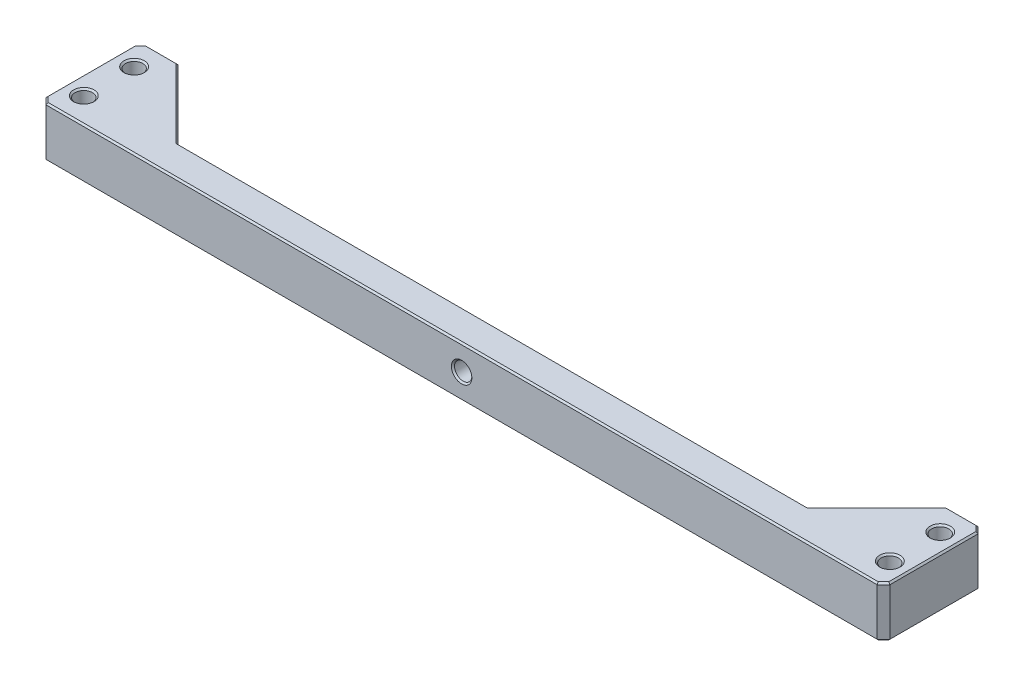
SolidWorks part; units mm, degrees
ref_plane "Front Plane" through (0, 0, 0) normal (0, 0, 1) x (1, 0, 0)
ref_plane "Top Plane" through (0, 0, 0) normal (0, 1, 0) x (1, 0, 0)
ref_plane "Right Plane" through (0, 0, 0) normal (1, 0, 0) x (0, 0, -1)
sketch "Sketch1" plane through (0, 0, 0) normal (0, 1, 0) x (1, 0, 0)
  line L0 (-106.3625, -6.35) -> (106.3625, -6.35)
  line L1 (106.3625, -6.35) -> (106.3625, 19.05)
  line L2 (106.3625, 19.05) -> (96.8375, 19.05)
  line L4 (79.375, 1.5875) -> (-79.375, 1.5875)
  line L6 (-96.8375, 19.05) -> (-106.3625, 19.05)
  line L7 (-106.3625, 19.05) -> (-106.3625, -6.35)
  line L8 (-96.8375, 19.05) -> (-79.375, 1.5875)
  line L9 (96.8375, 19.05) -> (79.375, 1.5875)
  circle A0 centre (-101.6, 0) radius 2.1828
  circle A1 centre (-101.6, 12.7) radius 2.1828
  circle A2 centre (101.6, 0) radius 2.1828
  circle A3 centre (101.6, 12.7) radius 2.1828
  point P17 (93.2798, 17.4625)
  dimension "D4" = 4.3656
  dimension "D5" = 4.3656
  dimension "D6" = 4.3656
  dimension "D7" = 4.3656
  dimension "D1" = 101.6
  dimension "D2" = 101.6
  dimension "D3" = 12.7
  dimension "D8" = 4.7625
  dimension "D9" = 45
  dimension "D10" = 6.35
  dimension "D11" = 6.35
  dimension "D12" = 7.9375
  dimension "D13" = 4.7625
  dimension "D14" = 6.35
  dimension "D15" = 45
  dimension "D16" = 4.7625
  dimension "D17" = 4.7625
extrude "Boss-Extrude1" add sketch "Sketch1" along normal blind 12.7
chamfer "Chamfer1" distance 1.5875 angle 45 4 edges at (106.3625, 6.35, -19.05) (106.3625, 6.35, 6.35) (-106.3625, 6.35, -19.05) (-106.3625, 6.35, 6.35)
sketch "Sketch2" plane through (0, 0, 6.35) normal (0, 0, 1) x (1, 0, 0)
  circle A0 centre (0, 6.35) radius 2.1828
  point P2 (0, 0)
  dimension "D2" = 4.3656
  dimension "D1" = 6.35
extrude "Cut-Extrude1" cut sketch "Sketch2" against normal through all both and the other way through all
chamfer "Chamfer2" distance 0.3969 angle 45 34 edges at (101.6, 0, -10.5172) (101.6, 0, 2.1828) (-101.6, 0, -10.5172) (-101.6, 0, 2.1828) (88.1063, 0, -10.3188) (0, 0, -1.5875) (-88.1062, 0, -10.3187) (-100.8062, 0, -19.05) (-105.5687, 0, -18.2562) (-106.3625, 0, -6.35) (-105.5688, 0, 5.5563) (0, 0, 6.35) (105.5687, 0, 5.5563) (106.3625, 0, -6.35) (105.5687, 0, -18.2563) (100.8062, 0, -19.05) (101.6, 12.7, -10.5172) (-101.6, 12.7, -10.5172) (105.5687, 12.7, 5.5563) (0, 12.7, 6.35) (-105.5688, 12.7, 5.5563) (-106.3625, 12.7, -6.35) (-105.5687, 12.7, -18.2562) (-100.8062, 12.7, -19.05) (-88.1062, 12.7, -10.3187) (0, 12.7, -1.5875) (88.1063, 12.7, -10.3188) (100.8062, 12.7, -19.05) (105.5687, 12.7, -18.2563) (106.3625, 12.7, -6.35) (-101.6, 12.7, 2.1828) (101.6, 12.7, 2.1828) (2.1828, 6.35, -1.5875) (-2.1828, 6.35, 6.35)
